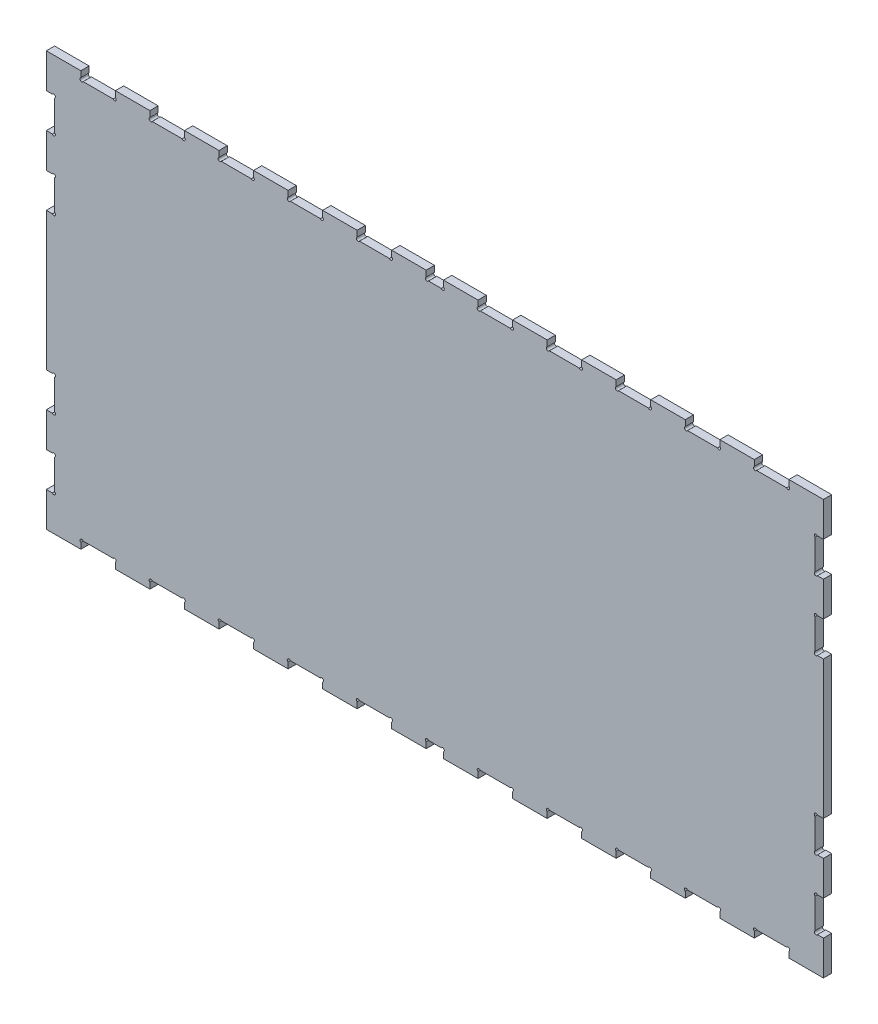
SolidWorks part; units mm, degrees
ref_plane "Front Plane" through (0, 0, 0) normal (0, 0, 1) x (1, 0, 0)
ref_plane "Top Plane" through (0, 0, 0) normal (0, 1, 0) x (1, 0, 0)
ref_plane "Right Plane" through (0, 0, 0) normal (1, 0, 0) x (0, 0, -1)
sketch "Sketch1" plane through (0, 0, 0) normal (0, 0, 1) x (1, 0, 0)
  line L0 (718.79, 153.6312) -> (668.79, 153.6312)
  line L1 (-106.21, -446.3688) -> (-56.21, -446.3688)
  line L2 (-406.21, 153.6312) -> (-406.21, 103.6312)
  line L3 (-406.21, -446.3688) -> (-356.21, -446.3688)
  line L4 (718.79, 153.6312) -> (718.79, 103.6312)
  line L5 (-56.21, -446.3688) -> (-56.21, -437.6473)
  line L6 (-52.9316, -434.3688) -> (-9.4885, -434.3688)
  line L7 (-6.21, -437.6473) -> (-6.21, -446.3688)
  line L8 (-6.21, -446.3688) -> (43.79, -446.3688)
  line L9 (43.79, -446.3688) -> (43.79, -437.6473)
  line L10 (47.0684, -434.3688) -> (90.5115, -434.3688)
  line L11 (93.79, -437.6473) -> (93.79, -446.3688)
  line L12 (93.79, -446.3688) -> (143.79, -446.3688)
  line L13 (143.79, -446.3688) -> (143.79, -437.6473)
  line L14 (147.0684, -434.3688) -> (165.5115, -434.3688)
  line L15 (168.79, -437.6473) -> (168.79, -446.3688)
  line L16 (168.79, -446.3688) -> (218.79, -446.3688)
  line L17 (-81.21, -446.3688) -> (-81.21, -388.8494) construction
  line L18 (-31.21, -434.3688) -> (-31.21, -383.2748) construction
  line L19 (18.79, -446.3688) -> (18.79, -371.3688) construction
  line L20 (68.79, -434.3688) -> (68.79, -370.1688) construction
  line L21 (118.79, -446.3688) -> (118.79, -368.1671) construction
  line L22 (668.79, -446.3688) -> (668.79, -437.6473)
  line L23 (665.5115, -434.3688) -> (622.0684, -434.3688)
  line L24 (618.79, -437.6473) -> (618.79, -446.3688)
  line L25 (568.79, -446.3688) -> (568.79, -437.6473)
  line L26 (565.5115, -434.3688) -> (522.0684, -434.3688)
  line L27 (518.79, -437.6473) -> (518.79, -446.3688)
  line L28 (468.79, -446.3688) -> (468.79, -437.6473)
  line L29 (465.5115, -434.3688) -> (422.0684, -434.3688)
  line L30 (418.79, -437.6473) -> (418.79, -446.3688)
  line L31 (368.79, -446.3688) -> (368.79, -437.6473)
  line L32 (365.5115, -434.3688) -> (322.0684, -434.3688)
  line L33 (318.79, -437.6473) -> (318.79, -446.3688)
  line L34 (268.79, -446.3688) -> (268.79, -437.6473)
  line L35 (265.5115, -434.3688) -> (222.0684, -434.3688)
  line L36 (218.79, -437.6473) -> (218.79, -446.3688)
  line L37 (668.79, -446.3688) -> (718.79, -446.3688)
  line L38 (568.79, -446.3688) -> (618.79, -446.3688)
  line L39 (468.79, -446.3688) -> (518.79, -446.3688)
  line L40 (368.79, -446.3688) -> (418.79, -446.3688)
  line L41 (268.79, -446.3688) -> (318.79, -446.3688)
  line L42 (-406.21, 82.6529) -> (493.79, 82.6529) construction
  line L43 (493.79, 82.6529) -> (43.79, 82.6529) construction
  line L44 (43.79, 82.6529) -> (43.79, 232.2142) construction
  line L45 (-406.21, -146.3688) -> (493.79, -146.3688) construction
  line L46 (-356.21, 153.6312) -> (-356.21, 144.9096)
  line L47 (-352.9316, 141.6312) -> (-309.4885, 141.6312)
  line L48 (-306.21, 144.9096) -> (-306.21, 153.6312)
  line L49 (-256.21, 153.6312) -> (-256.21, 144.9096)
  line L50 (-252.9316, 141.6312) -> (-209.4885, 141.6312)
  line L51 (-206.21, 144.9096) -> (-206.21, 153.6312)
  line L52 (-156.21, 153.6312) -> (-156.21, 144.9096)
  line L53 (-152.9316, 141.6312) -> (-109.4885, 141.6312)
  line L54 (-106.21, 144.9096) -> (-106.21, 153.6312)
  line L55 (-56.21, 153.6312) -> (-56.21, 144.9096)
  line L56 (-52.9316, 141.6312) -> (-9.4885, 141.6312)
  line L57 (-6.21, 144.9096) -> (-6.21, 153.6312)
  line L58 (43.79, 153.6312) -> (43.79, 144.9096)
  line L59 (47.0684, 141.6312) -> (90.5115, 141.6312)
  line L60 (93.79, 144.9096) -> (93.79, 153.6312)
  line L61 (-106.21, -437.6473) -> (-106.21, -446.3688)
  line L62 (-152.9316, -434.3688) -> (-109.4885, -434.3688)
  line L63 (-156.21, -446.3688) -> (-156.21, -437.6473)
  line L64 (-206.21, -437.6473) -> (-206.21, -446.3688)
  line L65 (-252.9316, -434.3688) -> (-209.4885, -434.3688)
  line L66 (-256.21, -446.3688) -> (-256.21, -437.6473)
  line L67 (-306.21, -437.6473) -> (-306.21, -446.3688)
  line L68 (-352.9316, -434.3688) -> (-309.4885, -434.3688)
  line L69 (-356.21, -446.3688) -> (-356.21, -437.6473)
  line L70 (143.79, 153.6312) -> (143.79, 144.9096)
  line L71 (147.0684, 141.6312) -> (165.5115, 141.6312)
  line L72 (168.79, 144.9096) -> (168.79, 153.6312)
  line L73 (-306.21, -446.3688) -> (-256.21, -446.3688)
  line L74 (-206.21, -446.3688) -> (-156.21, -446.3688)
  line L75 (218.79, 144.9096) -> (218.79, 153.6312)
  line L76 (-406.21, -396.3688) -> (-397.4885, -396.3688)
  line L77 (-402.8251, -396.3688) -> (-402.8251, -346.3688) construction
  line L78 (-397.4885, -346.3688) -> (-406.21, -346.3688)
  line L79 (-406.21, -396.3688) -> (-406.21, -446.3688)
  line L80 (-406.21, -296.3688) -> (-397.4885, -296.3688)
  line L81 (-394.21, -293.0904) -> (-394.21, -249.6473)
  line L82 (-397.4885, -246.3688) -> (-406.21, -246.3688)
  line L83 (-406.21, -296.3688) -> (-406.21, -346.3688)
  line L84 (-394.21, -396.3688) -> (-396.61, -396.3688) construction
  line L85 (-396.61, -396.3688) -> (-395.41, -396.3688) construction
  line L86 (-395.41, -396.3688) -> (-395.41, -394.7135) construction
  line L87 (-394.21, -396.3688) -> (-394.21, -393.9688) construction
  line L88 (-394.21, -393.9688) -> (-394.21, -395.1688) construction
  line L89 (-394.21, -395.1688) -> (-395.8428, -395.1688) construction
  line L90 (-394.21, -393.0904) -> (-394.21, -349.6473)
  line L91 (-402.8251, -346.3688) -> (-402.8251, -371.3688) construction
  line L92 (-402.8251, -371.3688) -> (-391.7132, -371.3688) construction
  line L93 (-400.6945, -346.3688) -> (-400.6945, -296.3688) construction
  line L94 (-400.6945, -296.3688) -> (-400.6945, -321.3688) construction
  line L95 (-400.6945, -321.3688) -> (-391.7132, -321.3688) construction
  line L96 (-400.6945, -296.3688) -> (-400.6945, -246.3688) construction
  line L97 (-400.6945, -246.3688) -> (-400.6945, -271.3688) construction
  line L98 (-400.6945, -271.3688) -> (-392.2754, -271.3688) construction
  line L99 (-397.4885, -46.3688) -> (-406.21, -46.3688)
  line L100 (-394.21, 0.3527) -> (-394.21, -43.0904)
  line L101 (-406.21, 3.6312) -> (-397.4885, 3.6312)
  line L102 (-397.4885, 53.6312) -> (-406.21, 53.6312)
  line L103 (-394.21, 100.3527) -> (-394.21, 56.9096)
  line L104 (-406.21, 103.6312) -> (-397.4885, 103.6312)
  line L105 (-406.21, 53.6312) -> (-406.21, 3.6312)
  line L106 (-406.21, -46.3688) -> (-406.21, -246.3688)
  line L107 (156.29, -446.3688) -> (156.29, 153.6312) construction
  line L108 (718.79, 103.6312) -> (710.0684, 103.6312)
  line L109 (706.79, 100.3527) -> (706.79, 56.9096)
  line L110 (710.0684, 53.6312) -> (718.79, 53.6312)
  line L111 (718.79, 3.6312) -> (710.0684, 3.6312)
  line L112 (706.79, 0.3527) -> (706.79, -43.0904)
  line L113 (710.0684, -46.3688) -> (718.79, -46.3688)
  line L114 (710.0684, -246.3688) -> (718.79, -246.3688)
  line L115 (706.79, -293.0904) -> (706.79, -249.6473)
  line L116 (718.79, -296.3688) -> (710.0684, -296.3688)
  line L117 (710.0684, -346.3688) -> (718.79, -346.3688)
  line L118 (706.79, -393.0904) -> (706.79, -349.6473)
  line L119 (718.79, -396.3688) -> (710.0684, -396.3688)
  line L120 (718.79, 53.6312) -> (718.79, 3.6312)
  line L121 (718.79, -46.3688) -> (718.79, -246.3688)
  line L122 (718.79, -396.3688) -> (718.79, -446.3688)
  line L123 (718.79, -296.3688) -> (718.79, -346.3688)
  line L124 (265.5115, 141.6312) -> (222.0684, 141.6312)
  line L125 (268.79, 153.6312) -> (268.79, 144.9096)
  line L126 (318.79, 144.9096) -> (318.79, 153.6312)
  line L127 (365.5115, 141.6312) -> (322.0684, 141.6312)
  line L128 (368.79, 153.6312) -> (368.79, 144.9096)
  line L129 (418.79, 144.9096) -> (418.79, 153.6312)
  line L130 (465.5115, 141.6312) -> (422.0684, 141.6312)
  line L131 (468.79, 153.6312) -> (468.79, 144.9096)
  line L132 (518.79, 144.9096) -> (518.79, 153.6312)
  line L133 (565.5115, 141.6312) -> (522.0684, 141.6312)
  line L134 (568.79, 153.6312) -> (568.79, 144.9096)
  line L135 (618.79, 144.9096) -> (618.79, 153.6312)
  line L136 (665.5115, 141.6312) -> (622.0684, 141.6312)
  line L137 (668.79, 153.6312) -> (668.79, 144.9096)
  line L138 (-356.21, 153.6312) -> (-406.21, 153.6312)
  line L139 (-256.21, 153.6312) -> (-306.21, 153.6312)
  line L140 (-156.21, 153.6312) -> (-206.21, 153.6312)
  line L141 (-56.21, 153.6312) -> (-106.21, 153.6312)
  line L142 (43.79, 153.6312) -> (-6.21, 153.6312)
  line L143 (143.79, 153.6312) -> (93.79, 153.6312)
  line L144 (218.79, 153.6312) -> (168.79, 153.6312)
  line L145 (318.79, 153.6312) -> (268.79, 153.6312)
  line L146 (418.79, 153.6312) -> (368.79, 153.6312)
  line L147 (518.79, 153.6312) -> (468.79, 153.6312)
  line L148 (618.79, 153.6312) -> (568.79, 153.6312)
  arc A0 (-56.21, -437.6473) -> (-52.9316, -434.3688) centre (-55.01, -435.5688) cw
  arc A1 (-6.21, -437.6473) -> (-9.4885, -434.3688) centre (-7.41, -435.5688) ccw
  arc A2 (43.79, -437.6473) -> (47.0684, -434.3688) centre (44.99, -435.5688) cw
  arc A3 (93.79, -437.6473) -> (90.5115, -434.3688) centre (92.59, -435.5688) ccw
  arc A4 (143.79, -437.6473) -> (147.0684, -434.3688) centre (144.99, -435.5688) cw
  arc A5 (168.79, -437.6473) -> (165.5115, -434.3688) centre (167.59, -435.5688) ccw
  arc A6 (668.79, -437.6473) -> (665.5115, -434.3688) centre (667.59, -435.5688) ccw
  arc A7 (618.79, -437.6473) -> (622.0684, -434.3688) centre (619.99, -435.5688) cw
  arc A8 (568.79, -437.6473) -> (565.5115, -434.3688) centre (567.59, -435.5688) ccw
  arc A9 (518.79, -437.6473) -> (522.0684, -434.3688) centre (519.99, -435.5688) cw
  arc A10 (468.79, -437.6473) -> (465.5115, -434.3688) centre (467.59, -435.5688) ccw
  arc A11 (418.79, -437.6473) -> (422.0684, -434.3688) centre (419.99, -435.5688) cw
  arc A12 (368.79, -437.6473) -> (365.5115, -434.3688) centre (367.59, -435.5688) ccw
  arc A13 (318.79, -437.6473) -> (322.0684, -434.3688) centre (319.99, -435.5688) cw
  arc A14 (268.79, -437.6473) -> (265.5115, -434.3688) centre (267.59, -435.5688) ccw
  arc A15 (218.79, -437.6473) -> (222.0684, -434.3688) centre (219.99, -435.5688) cw
  arc A16 (-356.21, 144.9096) -> (-352.9316, 141.6312) centre (-355.01, 142.8312) ccw
  arc A17 (-306.21, 144.9096) -> (-309.4885, 141.6312) centre (-307.41, 142.8312) cw
  arc A18 (-106.21, -437.6473) -> (-109.4885, -434.3688) centre (-107.41, -435.5688) ccw
  arc A19 (-156.21, -437.6473) -> (-152.9316, -434.3688) centre (-155.01, -435.5688) cw
  arc A20 (-206.21, -437.6473) -> (-209.4885, -434.3688) centre (-207.41, -435.5688) ccw
  arc A21 (-256.21, -437.6473) -> (-252.9316, -434.3688) centre (-255.01, -435.5688) cw
  arc A22 (-306.21, -437.6473) -> (-309.4885, -434.3688) centre (-307.41, -435.5688) ccw
  arc A23 (-356.21, -437.6473) -> (-352.9316, -434.3688) centre (-355.01, -435.5688) cw
  circle A24 centre (-394.21, -396.3688) radius 2.4 construction
  arc A25 (-397.4885, -396.3688) -> (-394.21, -393.0904) centre (-395.41, -395.1688) ccw
  arc A26 (-397.4885, -346.3688) -> (-394.21, -349.6473) centre (-395.41, -347.5688) cw
  arc A27 (-397.4885, -296.3688) -> (-394.21, -293.0904) centre (-395.41, -295.1688) ccw
  arc A28 (-397.4885, -246.3688) -> (-394.21, -249.6473) centre (-395.41, -247.5688) cw
  arc A29 (-397.4885, -46.3688) -> (-394.21, -43.0904) centre (-395.41, -45.1688) ccw
  arc A30 (-397.4885, 3.6312) -> (-394.21, 0.3527) centre (-395.41, 2.4312) cw
  arc A31 (-397.4885, 53.6312) -> (-394.21, 56.9096) centre (-395.41, 54.8312) ccw
  arc A32 (-397.4885, 103.6312) -> (-394.21, 100.3527) centre (-395.41, 102.4312) cw
  arc A33 (710.0684, 103.6312) -> (706.79, 100.3527) centre (707.99, 102.4312) ccw
  arc A34 (710.0684, 53.6312) -> (706.79, 56.9096) centre (707.99, 54.8312) cw
  arc A35 (710.0684, 3.6312) -> (706.79, 0.3527) centre (707.99, 2.4312) ccw
  arc A36 (710.0684, -46.3688) -> (706.79, -43.0904) centre (707.99, -45.1688) cw
  arc A37 (710.0684, -246.3688) -> (706.79, -249.6473) centre (707.99, -247.5688) ccw
  arc A38 (710.0684, -296.3688) -> (706.79, -293.0904) centre (707.99, -295.1688) cw
  arc A39 (710.0684, -346.3688) -> (706.79, -349.6473) centre (707.99, -347.5688) ccw
  arc A40 (710.0684, -396.3688) -> (706.79, -393.0904) centre (707.99, -395.1688) cw
  arc A41 (-256.21, 144.9096) -> (-252.9316, 141.6312) centre (-255.01, 142.8312) ccw
  arc A42 (-206.21, 144.9096) -> (-209.4885, 141.6312) centre (-207.41, 142.8312) cw
  arc A43 (-156.21, 144.9096) -> (-152.9316, 141.6312) centre (-155.01, 142.8312) ccw
  arc A44 (-106.21, 144.9096) -> (-109.4885, 141.6312) centre (-107.41, 142.8312) cw
  arc A45 (-56.21, 144.9096) -> (-52.9316, 141.6312) centre (-55.01, 142.8312) ccw
  arc A46 (-6.21, 144.9096) -> (-9.4885, 141.6312) centre (-7.41, 142.8312) cw
  arc A47 (43.79, 144.9096) -> (47.0684, 141.6312) centre (44.99, 142.8312) ccw
  arc A48 (93.79, 144.9096) -> (90.5115, 141.6312) centre (92.59, 142.8312) cw
  arc A49 (143.79, 144.9096) -> (147.0684, 141.6312) centre (144.99, 142.8312) ccw
  arc A50 (168.79, 144.9096) -> (165.5115, 141.6312) centre (167.59, 142.8312) cw
  arc A51 (218.79, 144.9096) -> (222.0684, 141.6312) centre (219.99, 142.8312) ccw
  arc A52 (268.79, 144.9096) -> (265.5115, 141.6312) centre (267.59, 142.8312) cw
  arc A53 (318.79, 144.9096) -> (322.0684, 141.6312) centre (319.99, 142.8312) ccw
  arc A54 (368.79, 144.9096) -> (365.5115, 141.6312) centre (367.59, 142.8312) cw
  arc A55 (418.79, 144.9096) -> (422.0684, 141.6312) centre (419.99, 142.8312) ccw
  arc A56 (468.79, 144.9096) -> (465.5115, 141.6312) centre (467.59, 142.8312) cw
  arc A57 (518.79, 144.9096) -> (522.0684, 141.6312) centre (519.99, 142.8312) ccw
  arc A58 (568.79, 144.9096) -> (565.5115, 141.6312) centre (567.59, 142.8312) cw
  arc A59 (618.79, 144.9096) -> (622.0684, 141.6312) centre (619.99, 142.8312) ccw
  arc A60 (668.79, 144.9096) -> (665.5115, 141.6312) centre (667.59, 142.8312) cw
  dimension "D18" = 12
  dimension "D7" = 200
  dimension "D8" = 50
  dimension "D14" = 4.8
  dimension "D15" = 4.8
  dimension "D1" = 1125
  dimension "D2" = 600
  dimension "D3" = 50
  dimension "D4" = 50
  dimension "D5" = 50
  dimension "D6" = 50
  dimension "D9" = 50
  dimension "D10" = 50
  dimension "D11" = 50
  dimension "D12" = 50
  dimension "D13" = 50
  dimension "D16" = 12.5
  dimension "D17" = 50
extrude "Boss-Extrude1" add sketch "Sketch1" along normal blind 12
